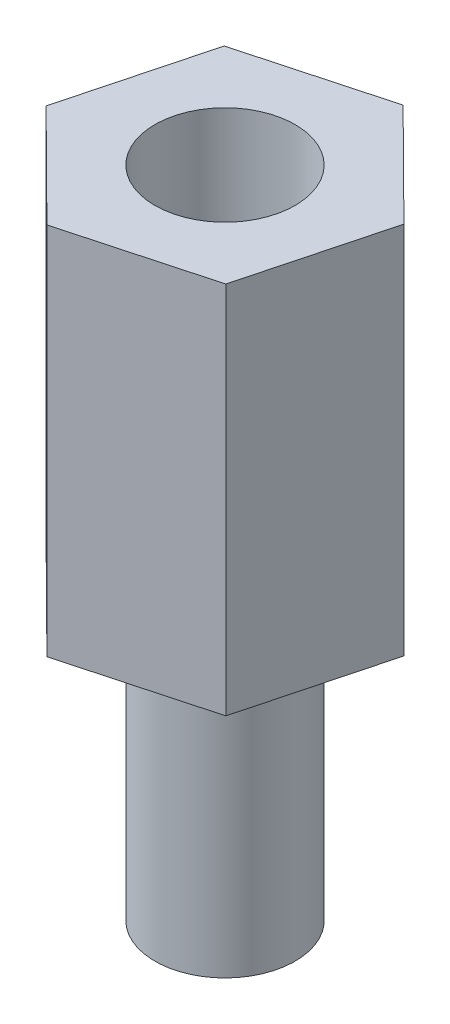
SolidWorks part; units mm, degrees
ref_plane "Front Plane" through (0, 0, 0) normal (0, 0, 1) x (1, 0, 0)
ref_plane "Top Plane" through (0, 0, 0) normal (0, 1, 0) x (1, 0, 0)
ref_plane "Right Plane" through (0, 0, 0) normal (1, 0, 0) x (0, 0, -1)
sketch "Sketch1" plane through (0, 0, 0) normal (0, 1, 0) x (1, 0, 0)
  line L1 (2.2134, -2.1957) -> (3.0082, 0.819)
  line L2 (3.0082, 0.819) -> (0.7948, 3.0147)
  line L3 (0.7948, 3.0147) -> (-2.2134, 2.1957)
  line L4 (-2.2134, 2.1957) -> (-3.0082, -0.819)
  line L5 (-3.0082, -0.819) -> (-0.7948, -3.0147)
  line L6 (-0.7948, -3.0147) -> (2.2134, -2.1957)
  circle A0 centre (0, 0) radius 2.7 construction
  dimension "D1" = 5.4
extrude "Boss-Extrude1" add sketch "Sketch1" along normal blind 8
sketch "Sketch2" plane through (0, 8, 0) normal (0, 1, 0) x (1, 0, 0)
  circle A0 centre (0, 0) radius 1.5
  dimension "D1" = 3
extrude "Cut-Extrude1" cut sketch "Sketch2" against normal blind 6
sketch "Sketch3" plane through (0, 0, 0) normal (0, -1, 0) x (1, 0, 0)
  circle A0 centre (0, 0) radius 1.5
  dimension "D1" = 3
extrude "Boss-Extrude2" add sketch "Sketch3" along normal blind 6
